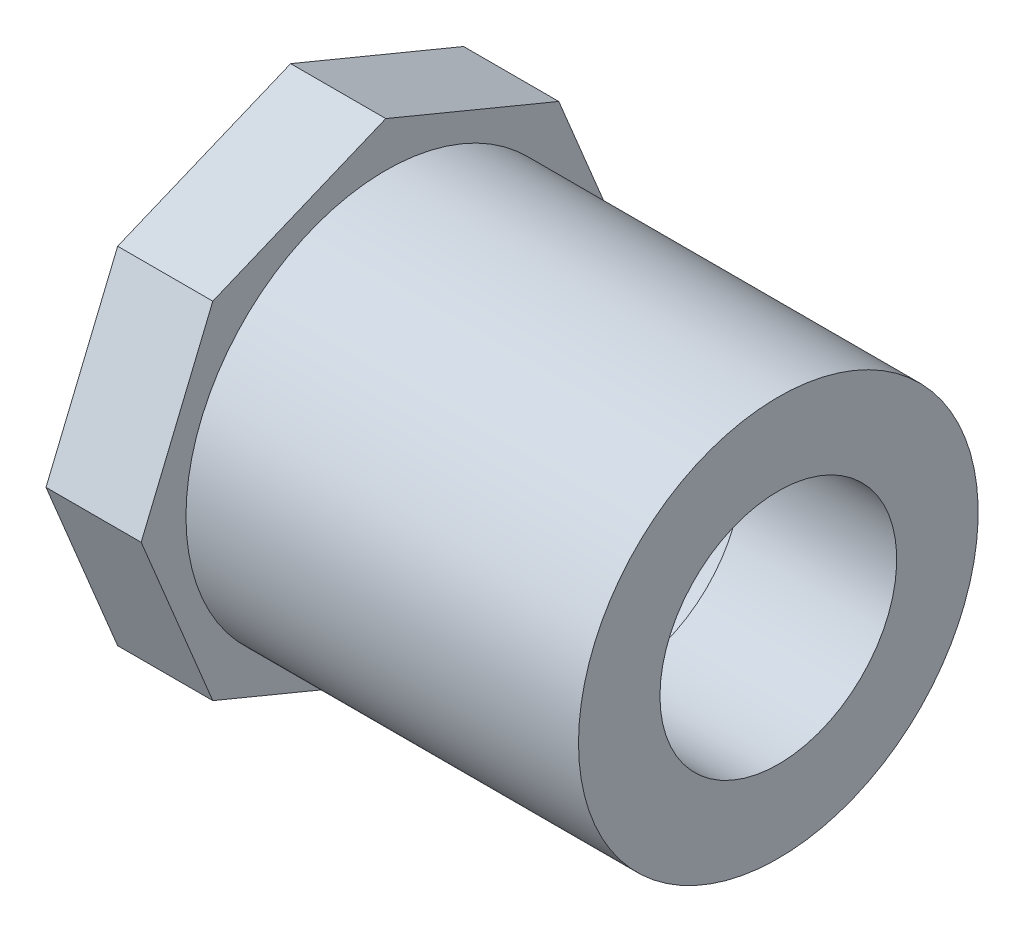
SolidWorks part; units mm, degrees
ref_plane "Front Plane" through (0, 0, 0) normal (0, 0, 1) x (1, 0, 0)
ref_plane "Top Plane" through (0, 0, 0) normal (0, 1, 0) x (1, 0, 0)
ref_plane "Right Plane" through (0, 0, 0) normal (1, 0, 0) x (0, 0, -1)
sketch "Sketch0" plane through (0, 0, 0) normal (0, 0, 1) x (1, 0, 0)
  line L0 (-32.5437, 0) -> (0, 0) construction
  line L2 (-18.2626, 13.335) -> (-18.2626, -13.335) construction
  line L3 (-26.1937, 15.0812) -> (-26.1937, -15.0812) construction
  line L5 (-10.3187, 10.6172) -> (-32.5437, 10.7696) construction
  line L6 (-10.3187, 10.6172) -> (-10.3187, -10.6172) construction
  line L7 (-10.3187, -10.6172) -> (-32.5437, -10.7696) construction
  line L8 (-32.5437, 10.7696) -> (-32.5437, -10.7696) construction
  line L14 (-10.3187, 7.8994) -> (-10.3187, -7.8994) construction
  line L21 (-32.5437, 0) -> (-10.3187, 0) construction
  point P12 (-18.2626, 0)
  point P27 (-26.1937, 0)
  dimension "A" = 32.5437
  dimension "OD A 2" = 21.5392
  dimension "OD B 2" = 21.2344
  dimension "ID 2" = 15.7988
  dimension "B" = 10.3187
  dimension "Pipe OD 1" = 26.67
  dimension "C 1" = 18.2626
  dimension "J" = 30.1625
  dimension "K" = 6.35
sketch "Sketch1" plane through (0, 0, 0) normal (0, 0, 1) x (1, 0, 0)
  line L0 (-32.5437, 0) -> (0, 0) construction
  line L1 (-32.5437, 0) -> (0, 0) construction
  line L2 (-32.5437, -13.335) -> (0, -13.335)
  line L3 (0, -7.8994) -> (0, -13.335)
  line L4 (-32.5437, -13.335) -> (-32.5437, -10.7696)
  line L5 (-32.5437, -10.7696) -> (-10.3187, -10.6172)
  line L6 (0, 0) -> (0, -7.8994) construction
  line L8 (-10.3187, -7.8994) -> (-10.3187, -10.6172)
  line L11 (-10.3187, -7.8994) -> (0, -7.8994)
revolve "Revolve1" add sketch "Sketch1" angle 360 about L1
sketch "Sketch2" plane through (-32.5437, 0, 0) normal (-1, 0, 0) x (0, 0, 1)
  line L0 (0, 0) -> (16.3238, 0) construction
  line L1 (16.3238, 0) -> (11.5427, 11.5427)
  line L2 (11.5427, 11.5427) -> (0, 16.3238)
  line L3 (0, 16.3238) -> (-11.5427, 11.5427)
  line L4 (-11.5427, 11.5427) -> (-16.3238, 0)
  line L5 (-16.3238, 0) -> (-11.5427, -11.5427)
  line L6 (-11.5427, -11.5427) -> (0, -16.3238)
  line L7 (0, -16.3238) -> (11.5427, -11.5427)
  line L8 (11.5427, -11.5427) -> (16.3238, 0)
  circle A0 centre (0, 0) radius 10.7696 construction
  circle A1 centre (0, 0) radius 10.7696
  circle A2 centre (0, 0) radius 15.0813 construction
extrude "Boss-Extrude1" add sketch "Sketch2" against normal up to vertex (6.35 mm away) up to point (-26.1937, 0, 0)
